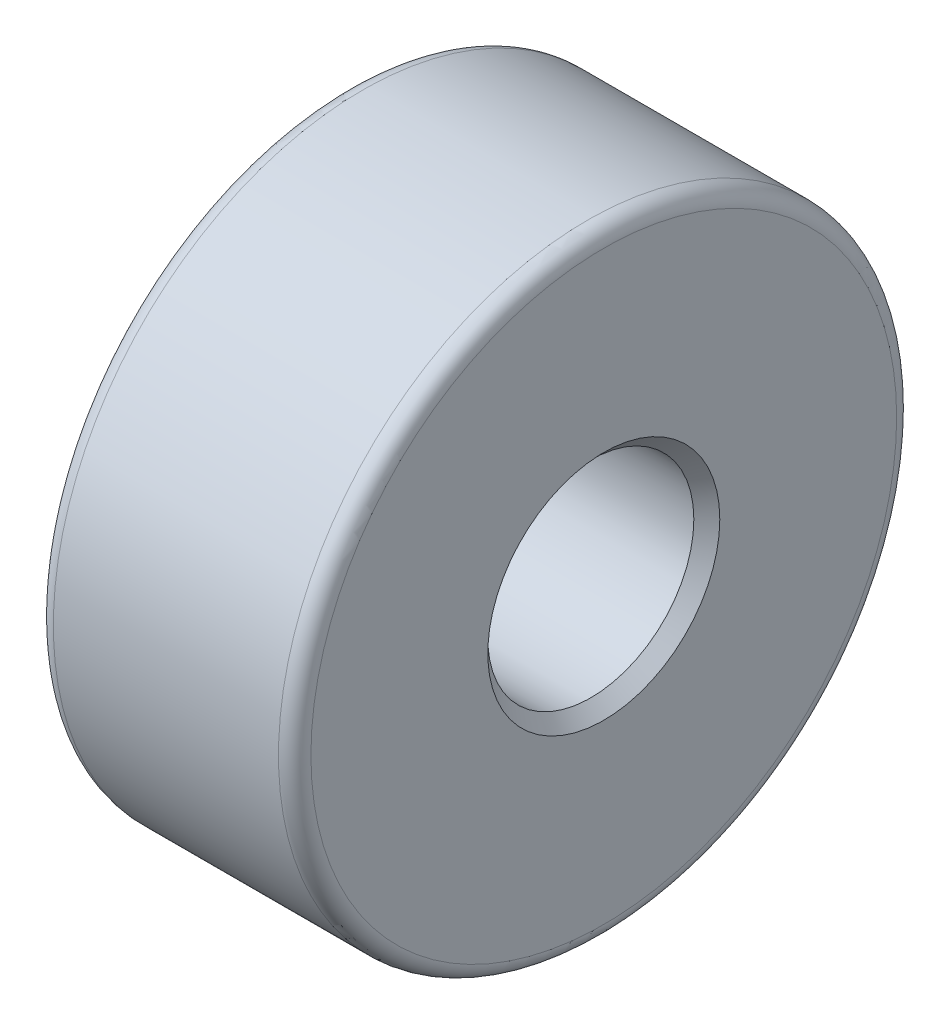
SolidWorks part; units mm, degrees
material "AISI 316 Annealed Stainless Steel Bar (SS)"
ref_plane "Front Plane" through (0, 0, 0) normal (0, 0, 1) x (1, 0, 0)
ref_plane "Top Plane" through (0, 0, 0) normal (0, 1, 0) x (1, 0, 0)
ref_plane "Right Plane" through (0, 0, 0) normal (1, 0, 0) x (0, 0, -1)
sketch "Sketch1" plane through (0, 0, 0) normal (1, 0, 0) x (0, 0, -1)
  circle A0 centre (0, 0) radius 4.7625
  circle A1 centre (0, 0) radius 1.5875
  dimension "D1" = 9.525
  dimension "D2" = 3.175
extrude "Boss-Extrude1" add sketch "Sketch1" along normal blind 3.9688
chamfer "Chamfer1" distance 0.2 angle 45 2 edges at (0, 0, -1.5875) (3.9688, 0, -1.5875)
fillet "Fillet1" radius 0.25 2 edges at (3.9688, 0, -4.7625) (0, 0, -4.7625)
